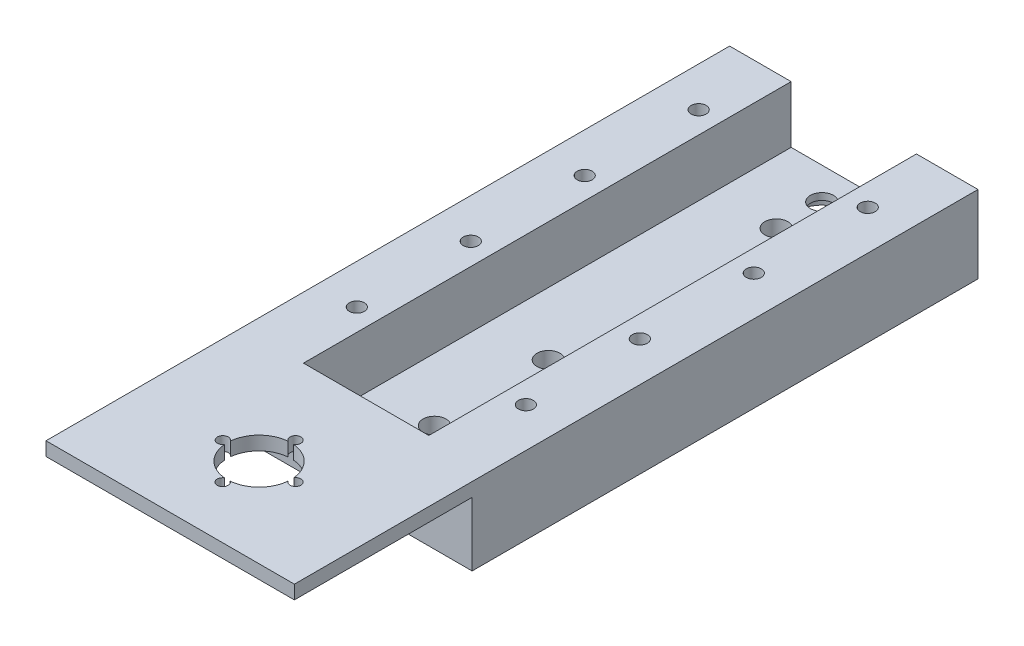
SolidWorks part; units mm, degrees
ref_plane "Front Plane" through (0, 0, 0) normal (0, 0, 1) x (1, 0, 0)
ref_plane "Top Plane" through (0, 0, 0) normal (0, 1, 0) x (1, 0, 0)
ref_plane "Right Plane" through (0, 0, 0) normal (1, 0, 0) x (0, 0, -1)
sketch "Sketch1" plane through (0, 0, 0) normal (0, 1, 0) x (1, 0, 0)
  line L1 (-40.6495, -11.3707) -> (13.8505, -11.3707)
  line L2 (-40.6495, -11.3707) -> (-40.6495, 99.6293)
  line L3 (-40.6495, 99.6293) -> (13.8505, 99.6293)
  line L4 (13.8505, -11.3707) -> (13.8505, 99.6293)
  dimension "D1" = 54.5
  dimension "D2" = 111
extrude "Boss-Extrude1" add sketch "Sketch1" along normal blind 4.5
sketch "Sketch2" plane through (0, 4.5, 0) normal (0, 1, 0) x (1, 0, 0)
  line L0 (13.8505, 99.6293) -> (-40.6495, 99.6293) construction
  line L1 (0.3505, 99.6293) -> (13.8505, 99.6293)
  line L2 (0.3505, 99.6293) -> (0.3505, -11.3707)
  line L3 (0.3505, -11.3707) -> (13.8505, -11.3707)
  line L4 (13.8505, 99.6293) -> (13.8505, -11.3707)
  line L5 (-40.6495, -11.3707) -> (13.8505, -11.3707) construction
  line L6 (-40.6495, 99.6293) -> (-27.1495, 99.6293)
  line L7 (-40.6495, 99.6293) -> (-40.6495, -11.3707)
  line L8 (-40.6495, -11.3707) -> (-27.1495, -11.3707)
  line L9 (-27.1495, 99.6293) -> (-27.1495, -11.3707)
  dimension "D1" = 13.5
  dimension "D2" = 13.5
extrude "Boss-Extrude2" add sketch "Sketch2" along normal blind 12.5 contours L7 L6 L9 L8 | L2 L1 L4 L3
hole_wizard "M4x0.7 Tapped Hole1" positions "3DSketch1" profile "Sketch3" tap size "M4x0.7" standard "ANSI Metric" end condition through all
sketch3d "3DSketch1"
  line L0 (-40.6495, 17, -99.6293) -> (-27.1495, 17, -99.6293) construction
  line L1 (-40.6495, 17, -99.6293) -> (-40.6495, 17, 11.3707) construction
  line L2 (-40.6495, 17, 11.3707) -> (-27.1495, 17, 11.3707) construction
  line L3 (0.3505, 17, -99.6293) -> (13.8505, 17, -99.6293) construction
  line L4 (13.8505, 17, -99.6293) -> (13.8505, 17, 11.3707) construction
  point P0 (-31.9495, 17, -9.1293)
  point P2 (-31.9495, 17, -34.1293)
  point P4 (-31.9495, 17, -59.1293)
  point P6 (-31.9495, 17, -84.1293)
  point P8 (5.1505, 17, -9.1293)
  point P10 (5.1505, 17, -34.1293)
  point P12 (5.1505, 17, -59.1293)
  point P14 (5.1505, 17, -84.1293)
  dimension "D1" = 15.5
  dimension "D2" = 8.7
  dimension "D3" = 25
  dimension "D4" = 8.7
  dimension "D5" = 25
  dimension "D6" = 8.7
  dimension "D7" = 25
  dimension "D8" = 8.7
  dimension "D9" = 20.5
  dimension "D10" = 15.5
  dimension "D11" = 8.7
  dimension "D12" = 25
  dimension "D13" = 8.7
  dimension "D14" = 25
  dimension "D15" = 8.7
  dimension "D16" = 8.7
  dimension "D17" = 25
sketch "Sketch3" plane through (-31.9495, 17, -9.1293) normal (1, 0, 0) x (0, 0, 1)
  line L0 (0, 0) -> (0, 17)
  line L1 (0, 17) -> (1.65, 17)
  line L2 (1.65, 17) -> (1.65, 0)
  line L5 (1.65, 0) -> (0, 0)
  line L11 (0, -6.35) -> (0, 107.95) construction
  dimension "Thru Tap Drill Dia." = 3.3
  dimension "Thru Tap Drill Depth" = 17
cosmetic thread "Hole Thread1" parameters "D2"=4
cosmetic thread "Hole Thread2" parameters "D2"=4
cosmetic thread "Hole Thread3" parameters "D2"=4
cosmetic thread "Hole Thread4" parameters "D2"=4
cosmetic thread "Hole Thread5" parameters "D2"=4
cosmetic thread "Hole Thread6" parameters "D2"=4
cosmetic thread "Hole Thread7" parameters "D2"=4
cosmetic thread "Hole Thread8" parameters "D2"=4
sketch "Sketch6" plane through (-27.1495, 0, 0) normal (1, 0, 0) x (0, 0, -1)
  line L0 (99.6293, 4.5) -> (-11.3707, 4.5) construction
  line L1 (-11.3707, 17) -> (-7.3707, 17)
  line L2 (-11.3707, 17) -> (-11.3707, 4.5)
  line L3 (-11.3707, 4.5) -> (-7.3707, 4.5)
  line L4 (-7.3707, 17) -> (-7.3707, 4.5)
  dimension "D1" = 4
extrude "Boss-Extrude3" add sketch "Sketch6" along normal blind 37
sketch "Sketch7" plane through (0, 0, 11.3707) normal (0, 0, 1) x (1, 0, 0)
  line L0 (13.8505, 17) -> (13.8505, 0) construction
  line L1 (-40.6495, 17) -> (13.8505, 17)
  line L2 (-40.6495, 17) -> (-40.6495, 14)
  line L3 (-40.6495, 14) -> (13.8505, 14)
  line L4 (13.8505, 17) -> (13.8505, 14)
  dimension "D1" = 3
extrude "Boss-Extrude5" add sketch "Sketch7" along normal blind 39
sketch "Sketch8" plane through (0, 17, 0) normal (0, 1, 0) x (1, 0, 0)
  line L1 (-40.6495, 99.6293) -> (-40.6495, -50.3707) construction
  circle A0 centre (-13.3995, -30.8707) radius 7
  dimension "D1" = 19.5
  dimension "D2" = 27.25
extrude "Cut-Extrude1" cut sketch "Sketch8" against normal blind 3 contours A0
hole_wizard "M2 Clearance Hole1" positions "3DSketch2" profile "Sketch9" hole size "M2" standard "ANSI Metric" end condition through all
sketch3d "3DSketch2"
  line L0 (13.8505, 17, 50.3707) -> (-40.6495, 17, 50.3707) construction
  line L1 (13.8505, 17, -99.6293) -> (13.8505, 17, 50.3707) construction
  point P0 (-21.3714, 17, 30.8479)
  point P2 (-13.3995, 17, 22.8707)
  point P4 (-13.3995, 17, 38.8707)
  point P12 (-5.4305, 17, 30.8451)
  dimension "D1" = 11.5
  dimension "D2" = 16
  dimension "D3" = 27.25
  dimension "D4" = 27.25
  dimension "D5" = 11.31
  dimension "D6" = 11.31
sketch "Sketch9" plane through (-21.3714, 17, 30.8479) normal (1, 0, 0) x (0, 0, 1)
  line L0 (0, 0) -> (0, 17)
  line L1 (0, 17) -> (1.2, 17)
  line L2 (1.2, 17) -> (1.2, 0)
  line L5 (1.2, 0) -> (0, 0)
  line L11 (0, -6.35) -> (0, 107.95) construction
  dimension "Thru Hole Dia." = 2.4
  dimension "Thru Hole Depth" = 17
hole_wizard "#8 (0.199) Diameter Hole1" positions "3DSketch4" profile "Sketch10" hole size "#8" standard "Progressive" end condition through all
sketch3d "3DSketch4"
  line L4 (0.3505, 4.5, -99.6293) -> (0.3505, 4.5, 7.3707) construction
  line L6 (0.3505, 4.5, 7.3707) -> (-27.1495, 4.5, 7.3707) construction
  line L7 (0.3505, 4.5, -99.6293) -> (-27.1495, 4.5, -99.6293) construction
  point P0 (-13.3995, 4.5, 2.3707)
  point P2 (-13.3995, 4.5, -7.6293)
  point P4 (-13.3995, 4.5, -32.6293)
  point P6 (-13.3995, 4.5, -82.6293)
  point P8 (-13.3995, 4.5, -92.6293)
  dimension "D1" = 13.75
  dimension "D2" = 13.75
  dimension "D4" = 13.75
  dimension "D3" = 13.75
  dimension "D5" = 13.75
  dimension "D6" = 5
  dimension "10" = 10
  dimension "D7" = 7
  dimension "D8" = 10
  dimension "D9" = 25
sketch "Sketch10" plane through (-13.3995, 4.5, 2.3707) normal (1, 0, 0) x (0, 0, 1)
  line L0 (0, 0) -> (0, 4.5)
  line L1 (0, 4.5) -> (2.5273, 4.5)
  line L2 (2.5273, 4.5) -> (2.5273, 0)
  line L5 (2.5273, 0) -> (0, 0)
  line L11 (0, -6.35) -> (0, 107.95) construction
  dimension "Thru Hole Dia." = 5.0546
  dimension "Thru Hole Depth" = 4.5
sketch "Sketch12" plane through (0, 0, 0) normal (0, -1, 0) x (-1, 0, 0)
  circle A2 centre (13.3995, 92.6293) radius 5.5
extrude "Cut-Extrude3" cut sketch "Sketch12" against normal blind 3
sketch "Sketch13" plane through (0, 0, 11.3707) normal (0, 0, 1) x (1, 0, 0)
  line L0 (-40.6495, 14) -> (13.8505, 14) construction
  line L1 (-27.1495, 14) -> (0.3505, 14)
  line L2 (-27.1495, 14) -> (-27.1495, 4.4863)
  line L3 (-27.1495, 4.4863) -> (0.3505, 4.4863)
  line L4 (0.3505, 14) -> (0.3505, 4.4863)
  line L6 (13.8505, 14) -> (13.8505, 0) construction
  line L7 (-40.6495, 14) -> (-40.6495, 0) construction
  dimension "D1" = 0
  dimension "D2" = 13.5
  dimension "D3" = 13.5
  dimension "D4" = 4.5
extrude "Cut-Extrude4" cut sketch "Sketch13" against normal blind 5
